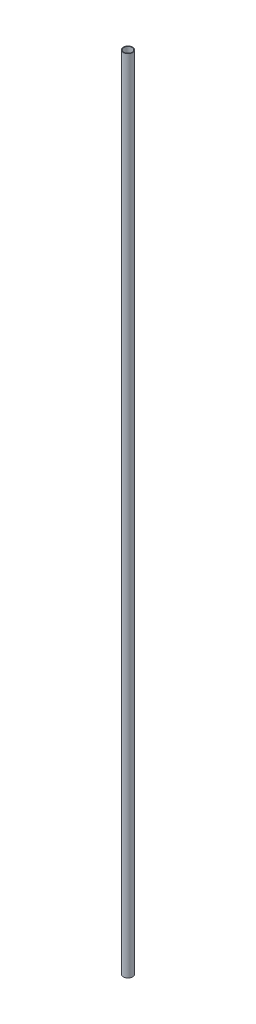
SolidWorks part; units mm, degrees
ref_plane "Front Plane" through (0, 0, 0) normal (0, 0, 1) x (1, 0, 0)
ref_plane "Top Plane" through (0, 0, 0) normal (0, 1, 0) x (1, 0, 0)
ref_plane "Right Plane" through (0, 0, 0) normal (1, 0, 0) x (0, 0, -1)
sketch "Sketch1" plane through (0, 0, 0) normal (0, 1, 0) x (1, 0, 0)
  circle A0 centre (0, 0) radius 0.7353
  circle A1 centre (0, 0) radius 0.6452
  dimension "D1" = 1.4707
  dimension "D2" = 1.2903
extrude "Boss-Extrude1" add sketch "Sketch1" along normal blind 125
sketch "Sketch2" plane through (0, 0, 0) normal (0, -1, 0) x (1, 0, 0)
  line L0 (0, 0) -> (0, -0.7353) construction
  line L1 (0.5, -0.7353) -> (-0.5, -0.7353)
  line L2 (0.5, -0.7353) -> (0.5, -0.3911)
  line L3 (0.5, -0.3911) -> (-0.5, -0.3911)
  line L4 (-0.5, -0.7353) -> (-0.5, -0.3911)
  circle A0 centre (0, 0) radius 0.7353 construction
  point P10 (0, -0.7353)
  dimension "D1" = 1
extrude "Cut-Extrude1" cut sketch "Sketch2" against normal blind 10
